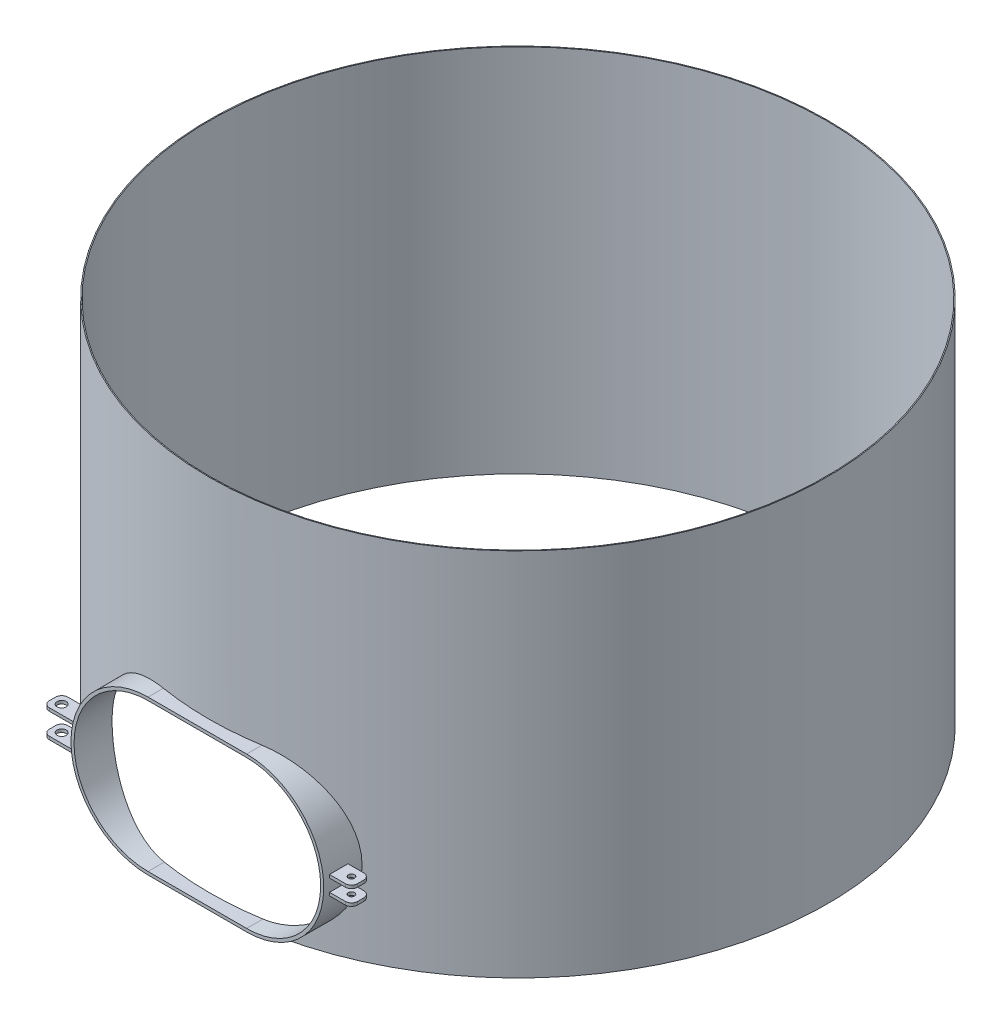
SolidWorks part; units mm, degrees
material "Wrought Stainless Steel"
ref_plane "Front Plane" through (0, 0, 0) normal (0, 0, 1) x (1, 0, 0)
ref_plane "Top Plane" through (0, 0, 0) normal (0, 1, 0) x (1, 0, 0)
ref_plane "Right Plane" through (0, 0, 0) normal (1, 0, 0) x (0, 0, -1)
sketch "Sketch1" plane through (0, 0, 0) normal (0, 1, 0) x (1, 0, 0)
  circle A0 centre (0, 0) radius 636.9837
  circle A1 centre (0, 0) radius 635
  dimension "D1" = 1.9837
  dimension "D2" = 1270
extrude "Boss-Extrude1" add sketch "Sketch1" along normal blind 762
ref_plane "Plane1" through (0, 0, 558.8) normal (0, 0, 1) x (1, 0, 0)
sketch "Sketch3" plane through (0, -431.8, 558.8) normal (0, 0, -1) x (1, 0, 0)
  line L1 (-101.6, -450.85) -> (101.6, -450.85)
  line L2 (-101.6, -444.5) -> (101.6, -444.5)
  line L3 (-101.6, -755.65) -> (101.6, -755.65)
  line L4 (-101.6, -762) -> (101.6, -762)
  line L5 (636.9837, -431.8) -> (-636.9837, -431.8) construction
  arc A0 (101.6, -450.85) -> (101.6, -755.65) centre (101.6, -603.25) cw
  arc A1 (-101.6, -450.85) -> (-101.6, -755.65) centre (-101.6, -603.25) ccw
  arc A2 (101.6, -444.5) -> (101.6, -762) centre (101.6, -603.25) cw
  arc A3 (-101.6, -444.5) -> (-101.6, -762) centre (-101.6, -603.25) ccw
  point P4 (0, -755.65)
  dimension "D3" = 6.35
  dimension "D6" = 203.2
  dimension "D1" = 304.8
  dimension "D2" = 203.2
  dimension "D4" = 12.7
  dimension "D5" = 6.35
extrude "Boss-Extrude2" add sketch "Sketch3" against normal blind 101.6
sketch "Sketch5" plane through (0, 762, 0) normal (0, 1, 0) x (1, 0, 0)
  circle A0 centre (0, 0) radius 635
extrude "Cut-Extrude2" cut sketch "Sketch5" against normal through all
ref_plane "Plane2" through (228.6, 0, 0) normal (1, 0, 0) x (0, 0, -1)
ref_plane "Plane3" through (-228.6, 0, 0) normal (1, 0, 0) x (0, 0, -1)
sketch "Sketch7" plane through (-228.6, 0, 0) normal (1, 0, 0) x (0, 0, -1)
  line L0 (-660.4, 330.2) -> (-628.8289, 330.2) construction
  line L1 (-609.6, 196.85) -> (-647.7, 196.85)
  line L2 (-609.6, 196.85) -> (-609.6, 190.5)
  line L3 (-609.6, 190.5) -> (-647.7, 190.5)
  line L4 (-647.7, 196.85) -> (-647.7, 190.5)
  line L5 (-609.6, 146.05) -> (-647.7, 146.05)
  line L6 (-609.6, 146.05) -> (-609.6, 139.7)
  line L7 (-609.6, 139.7) -> (-647.7, 139.7)
  line L8 (-647.7, 146.05) -> (-647.7, 139.7)
  line L10 (-660.4, 330.2) -> (-660.4, 12.7) construction
  dimension "D1" = 38.1
  dimension "D2" = 38.1
  dimension "D3" = 6.35
  dimension "D4" = 6.35
  dimension "D5" = 133.35
  dimension "D6" = 44.45
  dimension "D7" = 12.7
  dimension "D8" = 12.7
extrude "Boss-Extrude3" add sketch "Sketch7" against normal blind 101.6
sketch "Sketch8" plane through (0, 196.85, 0) normal (0, 1, 0) x (1, 0, 0)
  line L0 (-330.2, -609.6) -> (-330.2, -647.7) construction
  line L1 (-330.2, -647.7) -> (-258.3048, -647.7) construction
  circle A0 centre (-311.15, -628.65) radius 9.525
  dimension "D1" = 19.05
  dimension "D2" = 19.05
  dimension "D3" = 19.05
extrude "Cut-Extrude3" cut sketch "Sketch8" against normal blind 76.2
fillet "Fillet1" radius 12.7 4 edges at (-330.2, 142.875, 647.7) (-330.2, 142.875, 609.6) (-330.2, 193.675, 609.6) (-330.2, 193.675, 647.7)
sketch "Sketch9" plane through (228.6, 0, 0) normal (1, 0, 0) x (0, 0, -1)
  line L0 (-660.4, 330.2) -> (-660.4, 12.7) construction
  line L1 (-647.7, 187.96) -> (-609.6, 187.96)
  line L2 (-647.7, 187.96) -> (-647.7, 181.61)
  line L3 (-647.7, 181.61) -> (-609.6, 181.61)
  line L4 (-609.6, 187.96) -> (-609.6, 181.61)
  line L5 (-647.7, 156.21) -> (-609.6, 156.21)
  line L6 (-647.7, 156.21) -> (-647.7, 149.86)
  line L7 (-647.7, 149.86) -> (-609.6, 149.86)
  line L8 (-609.6, 156.21) -> (-609.6, 149.86)
  line L9 (-660.4, 330.2) -> (-628.8289, 330.2) construction
  dimension "D1" = 12.7
  dimension "D2" = 6.35
  dimension "D3" = 6.35
  dimension "D4" = 38.1
  dimension "D5" = 38.1
  dimension "D6" = 25.4
  dimension "D7" = 142.24
extrude "Boss-Extrude4" add sketch "Sketch9" along normal blind 76.2
sketch "Sketch4" plane through (0, 0, 660.4) normal (0, 0, 1) x (1, 0, 0)
  line L0 (-101.6, 323.85) -> (101.6, 323.85)
  line L1 (-101.6, 19.05) -> (101.6, 19.05)
  arc A0 (-101.6, 323.85) -> (-101.6, 19.05) centre (-101.6, 171.45) ccw
  arc A1 (101.6, 323.85) -> (101.6, 19.05) centre (101.6, 171.45) cw
extrude "Cut-Extrude1" cut sketch "Sketch4" against normal blind 101.6
sketch "Sketch10" plane through (0, 187.96, 0) normal (0, 1, 0) x (1, 0, 0)
  line L0 (304.8, -647.7) -> (259.4891, -647.7) construction
  circle A0 centre (285.75, -628.65) radius 6.35
  dimension "D1" = 12.7
  dimension "D2" = 19.05
  dimension "D3" = 19.05
extrude "Cut-Extrude4" cut sketch "Sketch10" against normal through all
fillet "Fillet2" radius 12.7 4 edges at (304.8, 153.035, 609.6) (304.8, 153.035, 647.7) (304.8, 184.785, 647.7) (304.8, 184.785, 609.6)
